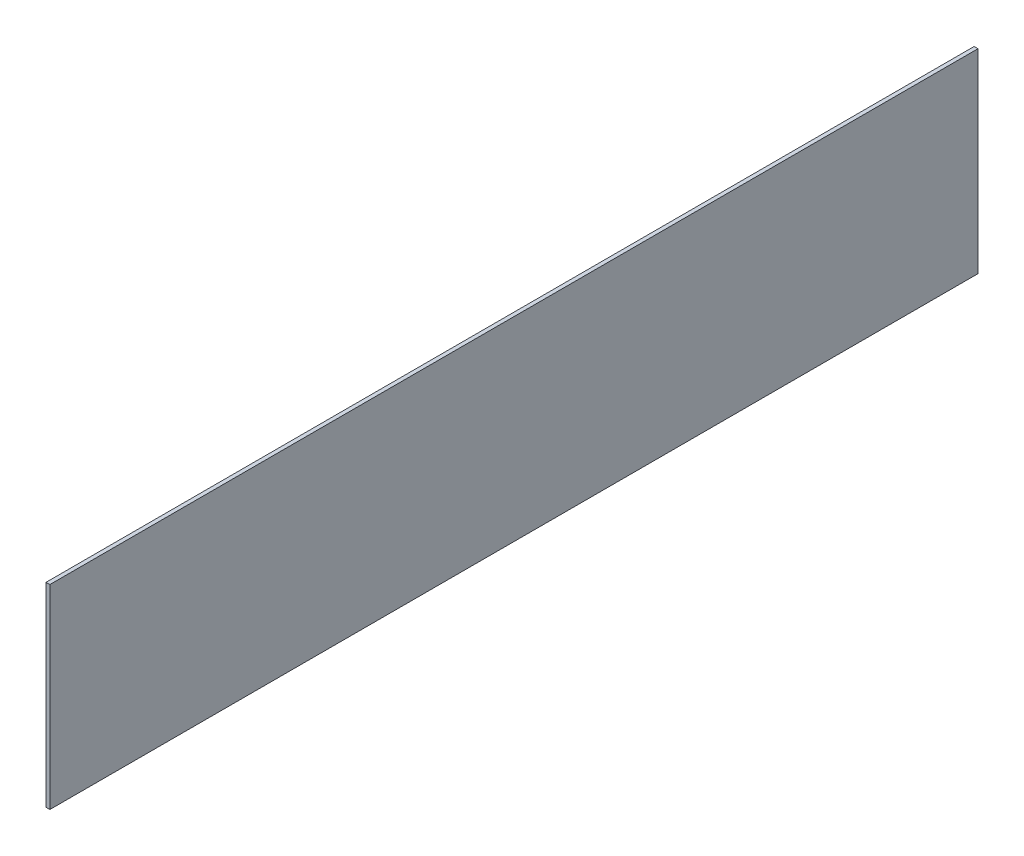
SolidWorks part; units mm, degrees
material "Plain Carbon Steel"
ref_plane "Front Plane" through (0, 0, 0) normal (0, 0, 1) x (1, 0, 0)
ref_plane "Top Plane" through (0, 0, 0) normal (0, 1, 0) x (1, 0, 0)
ref_plane "Right Plane" through (0, 0, 0) normal (1, 0, 0) x (0, 0, -1)
sketch "Sketch1" plane through (0, 0, 0) normal (1, 0, 0) x (0, 0, -1)
  line L1 (302.48, 63.5) -> (0, 63.5)
  line L2 (302.48, 63.5) -> (302.48, 0)
  line L3 (302.48, 0) -> (0, 0)
  line L4 (0, 63.5) -> (0, 0)
  dimension "D1" = 302.48
  dimension "D2" = 63.5
extrude "Boss-Extrude1" add sketch "Sketch1" along normal mid plane 1.2573
